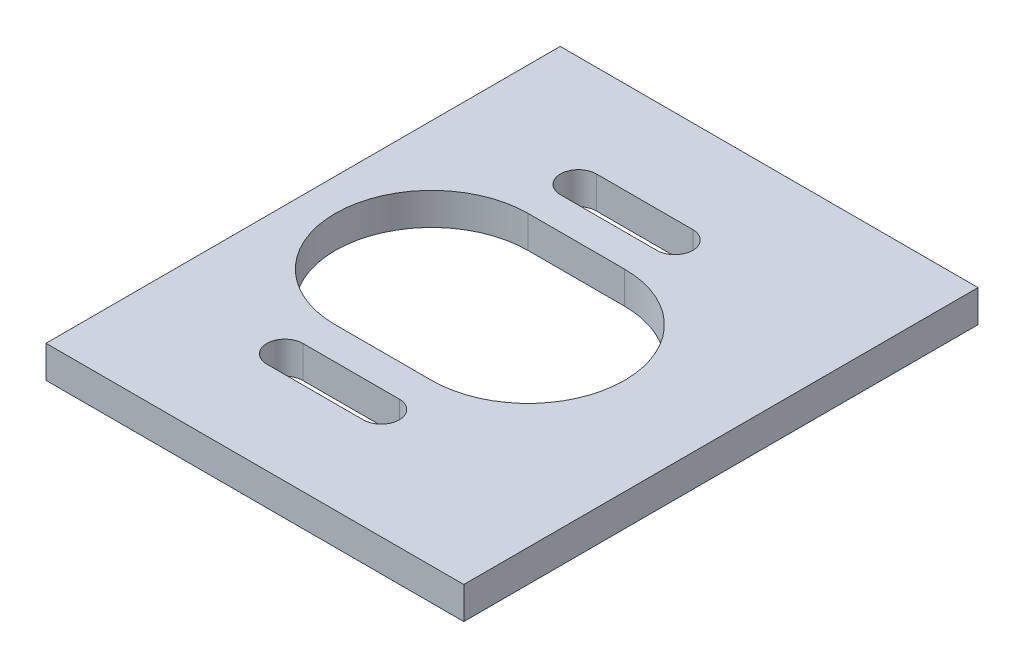
SolidWorks part; units mm, degrees
material "6061-T6 (SS)"
ref_plane "Front Plane" through (0, 0, 0) normal (0, 0, 1) x (1, 0, 0)
ref_plane "Top Plane" through (0, 0, 0) normal (0, 1, 0) x (1, 0, 0)
ref_plane "Right Plane" through (0, 0, 0) normal (1, 0, 0) x (0, 0, -1)
sketch "Sketch1" plane through (0, 0, 0) normal (0, 1, 0) x (1, 0, 0)
  line L1 (-88.9, 25.4) -> (88.9, 25.4)
  line L2 (-88.9, 25.4) -> (-88.9, -25.4)
  line L3 (-88.9, -25.4) -> (88.9, -25.4)
  line L4 (88.9, 25.4) -> (88.9, -25.4)
  line L5 (-88.9, 25.4) -> (88.9, -25.4) construction
  line L6 (-88.9, -25.4) -> (88.9, 25.4) construction
  point P0 (0, 0)
  dimension "D1" = 177.8
  dimension "D2" = 50.8
extrude "Boss-Extrude1" add sketch "Sketch1" along normal blind 3.175
sketch "Sketch2" plane through (0, 3.175, 0) normal (0, 1, 0) x (1, 0, 0)
  line L0 (-76.2, -14.5) -> (-66.675, -14.5) construction
  line L1 (-76.2, -12.722) -> (-66.675, -12.722)
  line L2 (-76.2, -16.278) -> (-66.675, -16.278)
  line L3 (-66.675, 14.5) -> (-76.2, 14.5) construction
  line L4 (-66.675, 12.722) -> (-76.2, 12.722)
  line L5 (-66.675, 16.278) -> (-76.2, 16.278)
  line L6 (-88.9, 25.4) -> (-88.9, -25.4) construction
  line L7 (-88.9, 25.4) -> (-76.2, 14.5) construction
  line L8 (-76.2, -14.5) -> (-88.9, -25.4) construction
  line L9 (-66.675, 0) -> (-76.2, 0) construction
  line L10 (-66.675, -9.525) -> (-76.2, -9.525)
  line L11 (-66.675, 9.525) -> (-76.2, 9.525)
  arc A0 (-76.2, -12.722) -> (-76.2, -16.278) centre (-76.2, -14.5) ccw
  arc A1 (-66.675, -16.278) -> (-66.675, -12.722) centre (-66.675, -14.5) ccw
  arc A2 (-66.675, 12.722) -> (-66.675, 16.278) centre (-66.675, 14.5) ccw
  arc A3 (-76.2, 16.278) -> (-76.2, 12.722) centre (-76.2, 14.5) ccw
  circle A4 centre (-44.45, 14.5) radius 1.65 construction
  arc A5 (-66.675, -9.525) -> (-66.675, 9.525) centre (-66.675, 0) ccw
  arc A6 (-76.2, 9.525) -> (-76.2, -9.525) centre (-76.2, 0) ccw
  point P2 (-71.4375, -14.5)
  point P7 (-71.4375, 14.5)
  point P16 (-44.45, 14.5)
  point P22 (-71.4375, 0)
  dimension "D2" = 9.525
  dimension "D1" = 3.556
  dimension "D3" = 12.7
  dimension "D4" = 19.05
extrude "Cut-Extrude1" cut sketch "Sketch2" against normal blind 3.175
mirror "Mirror1" about plane through (0, 0, 0) normal (1, 0, 0) of "Cut-Extrude1"
sketch "Sketch6" plane through (0, 3.175, 0) normal (0, 1, 0) x (1, 0, 0)
  line L0 (88.9, 25.4) -> (-88.9, 25.4) construction
  line L2 (53.975, -25.4) -> (-88.9, -25.4)
  line L3 (-88.9, -25.4) -> (-88.9, 25.4)
  line L4 (-88.9, 25.4) -> (53.975, 25.4)
  line L5 (53.975, 25.4) -> (53.975, -25.4)
  arc A0 (66.675, 9.525) -> (66.675, -9.525) centre (66.675, 0) ccw construction
  point P4 (0, 0)
  point P12 (57.15, 0)
  point P14 (53.975, 0)
  dimension "D1" = 3.175
extrude "Cut-Extrude3" cut sketch "Sketch6" against normal blind 3.175
sketch "Sketch8" plane through (88.9, 0, 0) normal (1, 0, 0) x (0, 0, -1)
  line L1 (-25.4, 3.175) -> (25.4, 3.175)
  line L2 (-25.4, 3.175) -> (-25.4, 0)
  line L3 (-25.4, 0) -> (25.4, 0)
  line L4 (25.4, 3.175) -> (25.4, 0)
extrude "Boss-Extrude2" add sketch "Sketch8" along normal blind 6.35
